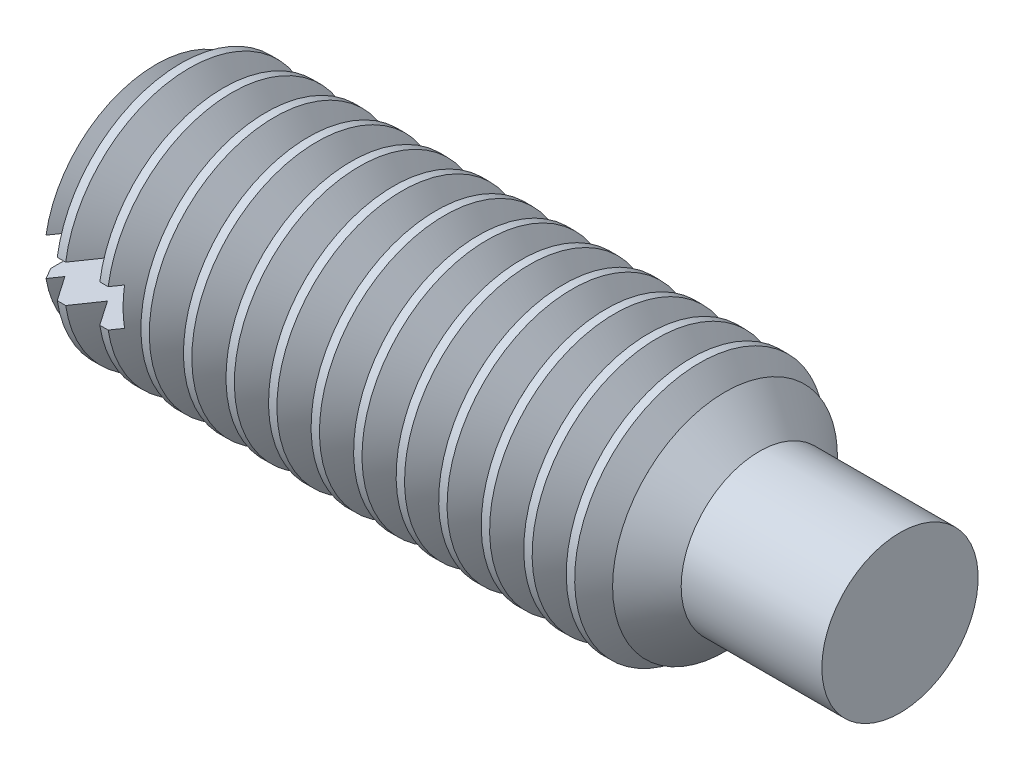
SolidWorks part; units mm, degrees
revolve "BaseBody" add sketch "BodySke"
sketch "BodySke" plane through (0, 0, 0) normal (0, 0, 1) x (1, 0, 0)
  line L0 (0.2252, -2) -> (19.05, -2) construction
  line L1 (9.75, 1.25) -> (12, 1.25)
  line L2 (0.2252, 2) -> (9, 2)
  line L3 (9.75, 1.25) -> (9, 2)
  line L4 (12, 0) -> (0, 0)
  line L5 (-12.7, 0) -> (88.9, 0) construction
  line L6 (0.7, 12.7) -> (0.7, -6.35) construction
  line L7 (12, 1.25) -> (12, 0)
  line L8 (9.75, -1.25) -> (12, -1.25) construction
  line L9 (0, 0) -> (0, 1.61)
  line L10 (0, 1.61) -> (0.2252, 2)
  dimension "Diameter" = 4
  dimension "Dog_dia" = 2.5
  dimension "Length" = 12
  dimension "Dog_len" = 2.25
  dimension "Advance" = 0.7
  dimension "Drive_ch_ang" = 60
  dimension "D1" = 45
  dimension "Minor_dia" = 3.22
cosmetic thread "ThreadCosmetic" [suppressed]
extrude "Slot" cut sketch "Sketch2" along normal blind 1.42
sketch "Sketch2" plane through (0, 0, 0) normal (1, 0, 0) x (0, 0, -1)
  line L1 (2, -0.3) -> (-2, -0.3)
  line L2 (2, -0.3) -> (2, 0.3)
  line L3 (2, 0.3) -> (-2, 0.3)
  line L4 (-2, -0.3) -> (-2, 0.3)
  dimension "D1" = 4
  dimension "Slot_width" = 0.6
  dimension "D3" = 2
  dimension "D2" = 0.3
ref_plane "Plane1" through (0, 0, 0) normal (0, 0, 1) x (1, 0, 0)
ref_plane "Plane2" through (0, 0, 0) normal (0, 1, 0) x (1, 0, 0)
ref_plane "Plane3" through (0, 0, 0) normal (1, 0, 0) x (0, 0, -1)
sketch "ThdSchSke" plane through (0, 0, 0) normal (0, 0, 1) x (1, 0, 0)
  line L0 (0.2252, -1.61) -> (-0.0479, -2)
  line L1 (0.2252, -1.61) -> (0.4982, -2)
  line L2 (0.4982, -2) -> (0.4982, -2.5)
  line L3 (-3.175, 0) -> (5.1513, 0) construction
  line L5 (0.4982, -2.5) -> (-0.0479, -2.5)
  line L6 (-0.0479, -2.5) -> (-0.0479, -2)
  line L7 (0.2252, -2) -> (0.2252, -0.3) construction
  dimension "Diameter" = 4
  dimension "Thread_minor" = 3.22
revolve "ThreadSchematic" cut sketch "ThdSchSke" angle 360 about L3
pattern_linear "ThdSchPat" count 14 spacing 0.6803 along (1, 0, 0) of "ThreadSchematic"
equation "\"D1@Sketch2\" = \"Diameter@BodySke\""
equation "\"D3@Sketch2\" = \"D1@Sketch2\" / 2"
equation "\"D2@Sketch2\" = \"Slot_width@Sketch2\" / 2"
equation "\"Thread_minor@ThreadCosmetic\" = \"Minor_dia@BodySke\""
equation "\"Thread_minor@ThdSchSke\" = \"Thread_minor@ThreadCosmetic\""
equation "\"Diameter@ThdSchSke\" = \"Diameter@BodySke\""
equation "\"Overcut@ThdSchSke\" = \"Diameter@BodySke\" * 1.25"
equation "\"Num_threads@ThdSchPat\" = int( (\"Length@BodySke\" - ( ( ( \"Diameter@BodySke\" - \"Minor_dia@BodySke\" ) * 0.5 ) / tan( \"Drive_ch_ang@BodySke\" * 0.017453292 ) ) - \"Dog_len@BodySke\" ) / \"Advance@BodySke\" + 0.999 )  + 1"
equation "\"Advance@ThdSchPat\" = (\"Length@BodySke\" - ( ( ( \"Diameter@BodySke\" - \"Minor_dia@BodySke\" ) * 0.5 ) / tan( \"Drive_ch_ang@BodySke\" * 0.017453292 ) ) - \"Dog_len@BodySke\" ) /  (\"Num_threads@ThdSchPat\" - 1) 'relax it"
equation "\"Num_threads@ThdSchPat\" = \"Num_threads@ThdSchPat\" - sgn( \"Num_threads@ThdSchPat\" - 1) '---chamfered tips only---"
